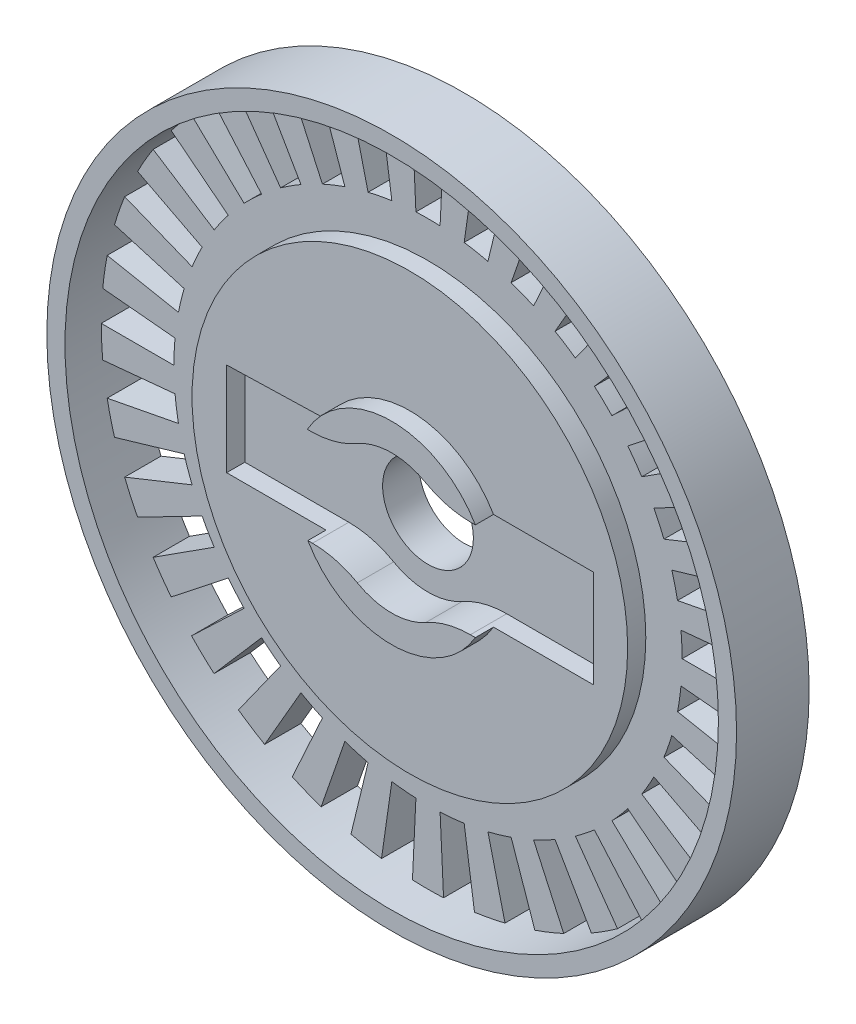
SolidWorks part; units mm, degrees
material "ABS"
ref_plane "Front Plane" through (0, 0, 0) normal (0, 0, 1) x (1, 0, 0)
ref_plane "Top Plane" through (0, 0, 0) normal (0, 1, 0) x (1, 0, 0)
ref_plane "Right Plane" through (0, 0, 0) normal (1, 0, 0) x (0, 0, -1)
sketch "Sketch1" plane through (0, 0, 0) normal (0, 0, 1) x (1, 0, 0)
  circle A0 centre (0, 0) radius 20
  dimension "D1" = 40
extrude "Boss-Extrude1" add sketch "Sketch1" along normal blind 4
sketch "Sketch2" plane through (0, 0, 4) normal (0, 0, 1) x (1, 0, 0)
  circle A0 centre (0, 0) radius 2.5
  dimension "D1" = 5
extrude "Cut-Extrude1" cut sketch "Sketch2" against normal blind 4
sketch "Sketch3" plane through (0, 0, 4) normal (0, 0, 1) x (1, 0, 0)
  line L6 (0, 0) -> (10.109, 0.0032) construction
  line L13 (10.075, 1.7016) -> (2.716, 2.6933) construction
  line L14 (10, 1.6361) -> (2.6806, 2.6224) construction
  line L15 (2.7051, -2.5972) -> (10, -5.8129) construction
  line L16 (2.7225, -2.6868) -> (10.075, -5.9279) construction
  line L17 (10.075, -5.9279) -> (10.075, 1.7016) construction
  line L18 (10, -5.8129) -> (10, 1.6361) construction
  line L19 (-10.075, 2.1965) -> (-2.9216, 2.4688) construction
  line L20 (-10, 2.1243) -> (-2.8855, 2.3951) construction
  line L21 (-2.7034, -2.5989) -> (-10, -1.9654) construction
  line L22 (-2.7378, -2.6712) -> (-10.075, -2.0342) construction
  line L23 (-10.075, -2.0342) -> (-10.075, 2.1965) construction
  line L24 (-10, -1.9654) -> (-10, 2.1243) construction
  line L25 (-2.7378, -2.6712) -> (-10.0936, -2.6712)
  line L26 (-10.0936, -2.6712) -> (-10.0936, 2.4688)
  line L29 (10.109, 0.0032) -> (10.109, -2.6868)
  line L30 (10.109, -2.6868) -> (2.7225, -2.6868)
  line L31 (2.7207, 2.6885) -> (10.109, 2.6885)
  line L32 (-2.7395, 2.6694) -> (-10.0936, 2.4688)
  line L33 (10.109, 2.6885) -> (10.109, 0.0032)
  arc A0 (-2.7034, -2.5989) -> (2.7051, -2.5972) centre (0, 0) ccw construction
  arc A1 (-2.7395, 2.6694) -> (2.7207, 2.6885) centre (0, 0) cw
  arc A4 (-2.7378, -2.6712) -> (2.7225, -2.6868) centre (0, 0) ccw
  arc A5 (2.6806, 2.6224) -> (-2.8855, 2.3951) centre (0, 0) ccw construction
  arc A6 (2.716, 2.6933) -> (-2.9216, 2.4688) centre (0, 0) ccw construction
  dimension "D1" = 5.4603
  dimension "D3" = 0.075
extrude "Cut-Extrude2" cut sketch "Sketch3" against normal blind 2
sketch "Sketch4" plane through (0, 0, 4) normal (0, 0, 1) x (1, 0, 0)
  line L0 (0, 0) -> (15, 0) construction
  line L1 (0, 0) -> (14.9321, 1.4258) construction
  line L2 (13.9366, 1.3308) -> (17.9185, 1.711)
  line L3 (14, 0) -> (18, 0)
  line L4 (-20, 0) -> (20, 0) construction
  line L5 (13.9366, -1.3308) -> (17.9185, -1.711)
  line L6 (13.747, -2.6495) -> (17.6747, -3.4065)
  line L7 (13.4329, -3.9443) -> (17.2709, -5.0712)
  line L8 (12.9972, -5.2033) -> (16.7106, -6.6899)
  line L9 (12.4437, -6.4152) -> (15.999, -8.2481)
  line L10 (11.7775, -7.569) -> (15.1426, -9.7315)
  line L11 (11.0047, -8.6542) -> (14.149, -11.1269)
  line L12 (10.1323, -9.6611) -> (13.0272, -12.4214)
  line L13 (9.1681, -10.5805) -> (11.7875, -13.6035)
  line L14 (8.1208, -11.4041) -> (10.441, -14.6624)
  line L15 (7, -12.1244) -> (9, -15.5885)
  line L16 (5.8158, -12.7348) -> (7.4775, -16.3734)
  line L17 (4.579, -13.23) -> (5.8872, -17.01)
  line L18 (3.3006, -13.6054) -> (4.2437, -17.4926)
  line L19 (1.9924, -13.8575) -> (2.5617, -17.8168)
  line L20 (0.6661, -13.9841) -> (0.8565, -17.9796)
  line L21 (-0.6661, -13.9841) -> (-0.8565, -17.9796)
  line L22 (-1.9924, -13.8575) -> (-2.5617, -17.8168)
  line L23 (-3.3006, -13.6054) -> (-4.2437, -17.4926)
  line L24 (-4.579, -13.23) -> (-5.8872, -17.01)
  line L25 (-5.8158, -12.7348) -> (-7.4775, -16.3734)
  line L26 (-7, -12.1244) -> (-9, -15.5885)
  line L27 (-8.1208, -11.4041) -> (-10.441, -14.6624)
  line L28 (-9.1681, -10.5805) -> (-11.7875, -13.6035)
  line L29 (-10.1323, -9.6611) -> (-13.0272, -12.4214)
  line L30 (-11.0047, -8.6542) -> (-14.149, -11.1269)
  line L31 (-11.7775, -7.569) -> (-15.1426, -9.7315)
  line L32 (-12.4437, -6.4152) -> (-15.999, -8.2481)
  line L33 (-12.9972, -5.2033) -> (-16.7106, -6.6899)
  line L34 (-13.4329, -3.9443) -> (-17.2709, -5.0712)
  line L35 (-13.747, -2.6495) -> (-17.6747, -3.4065)
  line L36 (-13.9366, -1.3308) -> (-17.9185, -1.711)
  line L37 (-14, 0) -> (-18, 0)
  line L38 (-13.9366, 1.3308) -> (-17.9185, 1.711)
  line L39 (-13.747, 2.6495) -> (-17.6747, 3.4065)
  line L40 (-13.4329, 3.9443) -> (-17.2709, 5.0712)
  line L41 (-12.9972, 5.2033) -> (-16.7106, 6.6899)
  line L42 (-12.4437, 6.4152) -> (-15.999, 8.2481)
  line L43 (-11.7775, 7.569) -> (-15.1426, 9.7315)
  line L44 (-11.0047, 8.6542) -> (-14.149, 11.1269)
  line L45 (-10.1323, 9.6611) -> (-13.0272, 12.4214)
  line L46 (-9.1681, 10.5805) -> (-11.7875, 13.6035)
  line L47 (-8.1208, 11.4041) -> (-10.441, 14.6624)
  line L48 (-7, 12.1244) -> (-9, 15.5885)
  line L49 (-5.8158, 12.7348) -> (-7.4775, 16.3734)
  line L50 (-4.579, 13.23) -> (-5.8872, 17.01)
  line L51 (-3.3006, 13.6054) -> (-4.2437, 17.4926)
  line L52 (-1.9924, 13.8575) -> (-2.5617, 17.8168)
  line L53 (-0.6661, 13.9841) -> (-0.8565, 17.9796)
  line L54 (0.6661, 13.9841) -> (0.8565, 17.9796)
  line L55 (1.9924, 13.8575) -> (2.5617, 17.8168)
  line L56 (3.3006, 13.6054) -> (4.2437, 17.4926)
  line L57 (4.579, 13.23) -> (5.8872, 17.01)
  line L58 (5.8158, 12.7348) -> (7.4775, 16.3734)
  line L59 (7, 12.1244) -> (9, 15.5885)
  line L60 (8.1208, 11.4041) -> (10.441, 14.6624)
  line L61 (9.1681, 10.5805) -> (11.7875, 13.6035)
  line L62 (10.1323, 9.6611) -> (13.0272, 12.4214)
  line L63 (11.0047, 8.6542) -> (14.149, 11.1269)
  line L64 (11.7775, 7.569) -> (15.1426, 9.7315)
  line L65 (12.4437, 6.4152) -> (15.999, 8.2481)
  line L66 (12.9972, 5.2033) -> (16.7106, 6.6899)
  line L67 (13.4329, 3.9443) -> (17.2709, 5.0712)
  line L68 (13.747, 2.6495) -> (17.6747, 3.4065)
  line L69 (0, 0) -> (19.3185, -5.1764) construction
  line L70 (0, 0) -> (-19.3185, -5.1764) construction
  circle A0 centre (0, 0) radius 15 construction
  arc A1 (14, 0) -> (13.9366, 1.3308) centre (0, 0) ccw construction
  arc A2 (18, 0) -> (17.9185, 1.711) centre (0, 0) ccw
  arc A3 (13.9366, 1.3308) -> (14, 0) centre (0, 0) cw
  circle A4 centre (0, 0) radius 20 construction
  arc A5 (17.6747, -3.4065) -> (17.9185, -1.711) centre (0, 0) ccw
  arc A6 (13.9366, -1.3308) -> (13.747, -2.6495) centre (0, 0) cw
  arc A7 (16.7106, -6.6899) -> (17.2709, -5.0712) centre (0, 0) ccw
  arc A8 (13.4329, -3.9443) -> (12.9972, -5.2033) centre (0, 0) cw
  arc A9 (15.1426, -9.7315) -> (15.999, -8.2481) centre (0, 0) ccw
  arc A10 (12.4437, -6.4152) -> (11.7775, -7.569) centre (0, 0) cw
  arc A11 (13.0272, -12.4214) -> (14.149, -11.1269) centre (0, 0) ccw
  arc A12 (11.0047, -8.6542) -> (10.1323, -9.6611) centre (0, 0) cw
  arc A13 (10.441, -14.6624) -> (11.7875, -13.6035) centre (0, 0) ccw
  arc A14 (9.1681, -10.5805) -> (8.1208, -11.4041) centre (0, 0) cw
  arc A15 (7.4775, -16.3734) -> (9, -15.5885) centre (0, 0) ccw
  arc A16 (7, -12.1244) -> (5.8158, -12.7348) centre (0, 0) cw
  arc A17 (4.2437, -17.4926) -> (5.8872, -17.01) centre (0, 0) ccw
  arc A18 (4.579, -13.23) -> (3.3006, -13.6054) centre (0, 0) cw
  arc A19 (0.8565, -17.9796) -> (2.5617, -17.8168) centre (0, 0) ccw
  arc A20 (1.9924, -13.8575) -> (0.6661, -13.9841) centre (0, 0) cw
  arc A21 (-2.5617, -17.8168) -> (-0.8565, -17.9796) centre (0, 0) ccw
  arc A22 (-0.6661, -13.9841) -> (-1.9924, -13.8575) centre (0, 0) cw
  arc A23 (-5.8872, -17.01) -> (-4.2437, -17.4926) centre (0, 0) ccw
  arc A24 (-3.3006, -13.6054) -> (-4.579, -13.23) centre (0, 0) cw
  arc A25 (-9, -15.5885) -> (-7.4775, -16.3734) centre (0, 0) ccw
  arc A26 (-5.8158, -12.7348) -> (-7, -12.1244) centre (0, 0) cw
  arc A27 (-11.7875, -13.6035) -> (-10.441, -14.6624) centre (0, 0) ccw
  arc A28 (-8.1208, -11.4041) -> (-9.1681, -10.5805) centre (0, 0) cw
  arc A29 (-14.149, -11.1269) -> (-13.0272, -12.4214) centre (0, 0) ccw
  arc A30 (-10.1323, -9.6611) -> (-11.0047, -8.6542) centre (0, 0) cw
  arc A31 (-15.999, -8.2481) -> (-15.1426, -9.7315) centre (0, 0) ccw
  arc A32 (-11.7775, -7.569) -> (-12.4437, -6.4152) centre (0, 0) cw
  arc A33 (-17.2709, -5.0712) -> (-16.7106, -6.6899) centre (0, 0) ccw
  arc A34 (-12.9972, -5.2033) -> (-13.4329, -3.9443) centre (0, 0) cw
  arc A35 (-17.9185, -1.711) -> (-17.6747, -3.4065) centre (0, 0) ccw
  arc A36 (-13.747, -2.6495) -> (-13.9366, -1.3308) centre (0, 0) cw
  arc A37 (-17.9185, 1.711) -> (-18, 0) centre (0, 0) ccw
  arc A38 (-14, 0) -> (-13.9366, 1.3308) centre (0, 0) cw
  arc A39 (-17.2709, 5.0712) -> (-17.6747, 3.4065) centre (0, 0) ccw
  arc A40 (-13.747, 2.6495) -> (-13.4329, 3.9443) centre (0, 0) cw
  arc A41 (-15.999, 8.2481) -> (-16.7106, 6.6899) centre (0, 0) ccw
  arc A42 (-12.9972, 5.2033) -> (-12.4437, 6.4152) centre (0, 0) cw
  arc A43 (-14.149, 11.1269) -> (-15.1426, 9.7315) centre (0, 0) ccw
  arc A44 (-11.7775, 7.569) -> (-11.0047, 8.6542) centre (0, 0) cw
  arc A45 (-11.7875, 13.6035) -> (-13.0272, 12.4214) centre (0, 0) ccw
  arc A46 (-10.1323, 9.6611) -> (-9.1681, 10.5805) centre (0, 0) cw
  arc A47 (-9, 15.5885) -> (-10.441, 14.6624) centre (0, 0) ccw
  arc A48 (-8.1208, 11.4041) -> (-7, 12.1244) centre (0, 0) cw
  arc A49 (-5.8872, 17.01) -> (-7.4775, 16.3734) centre (0, 0) ccw
  arc A50 (-5.8158, 12.7348) -> (-4.579, 13.23) centre (0, 0) cw
  arc A51 (-2.5617, 17.8168) -> (-4.2437, 17.4926) centre (0, 0) ccw
  arc A52 (-3.3006, 13.6054) -> (-1.9924, 13.8575) centre (0, 0) cw
  arc A53 (0.8565, 17.9796) -> (-0.8565, 17.9796) centre (0, 0) ccw
  arc A54 (-0.6661, 13.9841) -> (0.6661, 13.9841) centre (0, 0) cw
  arc A55 (4.2437, 17.4926) -> (2.5617, 17.8168) centre (0, 0) ccw
  arc A56 (1.9924, 13.8575) -> (3.3006, 13.6054) centre (0, 0) cw
  arc A57 (7.4775, 16.3734) -> (5.8872, 17.01) centre (0, 0) ccw
  arc A58 (4.579, 13.23) -> (5.8158, 12.7348) centre (0, 0) cw
  arc A59 (10.441, 14.6624) -> (9, 15.5885) centre (0, 0) ccw
  arc A60 (7, 12.1244) -> (8.1208, 11.4041) centre (0, 0) cw
  arc A61 (13.0272, 12.4214) -> (11.7875, 13.6035) centre (0, 0) ccw
  arc A62 (9.1681, 10.5805) -> (10.1323, 9.6611) centre (0, 0) cw
  arc A63 (15.1426, 9.7315) -> (14.149, 11.1269) centre (0, 0) ccw
  arc A64 (11.0047, 8.6542) -> (11.7775, 7.569) centre (0, 0) cw
  arc A65 (16.7106, 6.6899) -> (15.999, 8.2481) centre (0, 0) ccw
  arc A66 (12.4437, 6.4152) -> (12.9972, 5.2033) centre (0, 0) cw
  arc A67 (17.6747, 3.4065) -> (17.2709, 5.0712) centre (0, 0) ccw
  arc A68 (13.4329, 3.9443) -> (13.747, 2.6495) centre (0, 0) cw
  point P15 (0, 0)
  point P114 (0, 0)
  point P146 (0, 0)
  dimension "D1" = 5.455
  dimension "D3" = 14
  dimension "D5" = 15
  dimension "D6" = 15
  dimension "D2" = 4
  dimension "D4" = 33
extrude "Cut-Extrude3" cut sketch "Sketch4" against normal blind 4
sketch "Sketch5" plane through (0, 0, 4) normal (0, 0, 1) x (1, 0, 0)
  circle A0 centre (0, 0) radius 12
  circle A2 centre (0, 0) radius 18
  arc A4 (14, 0) -> (13.9366, 1.3308) centre (0, 0) ccw construction
  dimension "D1" = 2
  dimension "D2" = 6
extrude "Cut-Extrude4" cut sketch "Sketch5" against normal blind 2
sketch "Sketch6" plane through (0, 0, 4) normal (0, 0, 1) x (1, 0, 0)
  circle A0 centre (0, 0) radius 13.3357
  circle A1 centre (0, 0) radius 5.3357
  dimension "D1" = 8
extrude "Cut-Extrude5" cut sketch "Sketch6" against normal blind 1
fillet "Fillet2" radius 5 4 edges at (-2.7395, 2.6694, 3) (2.7207, 2.6885, 3) (2.7225, -2.6868, 3) (-2.7378, -2.6712, 3)
sketch "Sketch7" plane through (0, 0, 0) normal (0, 0, -1) x (-1, 0, 0)
  circle A0 centre (0, 0) radius 19
  circle A1 centre (0, 0) radius 20 construction
  circle A2 centre (0, 0) radius 20
  dimension "D1" = 1
extrude "Cut-Extrude6" cut sketch "Sketch7" against normal blind 10
